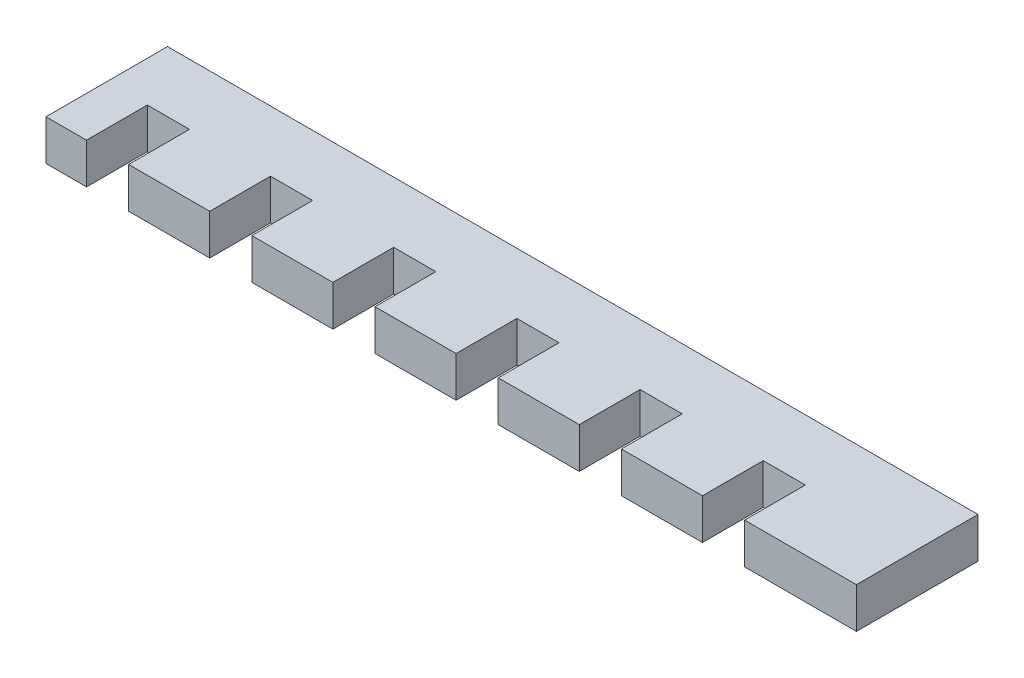
SolidWorks part; units mm, degrees
ref_plane "Front Plane" through (0, 0, 0) normal (0, 0, 1) x (1, 0, 0)
ref_plane "Top Plane" through (0, 0, 0) normal (0, 1, 0) x (1, 0, 0)
ref_plane "Right Plane" through (0, 0, 0) normal (1, 0, 0) x (0, 0, -1)
sketch "Sketch1" plane through (0, 0, 0) normal (0, 1, 0) x (1, 0, 0)
  line L1 (-50, 7.5) -> (50, 7.5)
  line L2 (-50, 7.5) -> (-50, -7.5)
  line L3 (-50, -7.5) -> (50, -7.5)
  line L4 (50, 7.5) -> (50, -7.5)
  line L5 (-50, 7.5) -> (50, -7.5) construction
  line L6 (-50, -7.5) -> (50, 7.5) construction
  point P0 (0, 0)
  dimension "D1" = 100
  dimension "D2" = 15
extrude "Boss-Extrude1" add sketch "Sketch1" along normal blind 5
sketch "Sketch2" plane through (0, 0, 0) normal (0, 1, 0) x (1, 0, 0)
  line L0 (-50, -7.5) -> (50, -7.5) construction
  line L1 (-45, -7.5) -> (-39.8, -7.5)
  line L2 (-45, -7.5) -> (-45, 0)
  line L3 (-45, 0) -> (-39.8, 0)
  line L4 (-39.8, -7.5) -> (-39.8, 0)
  line L5 (-50, 7.5) -> (-50, -7.5) construction
  line L8 (-29.8, -7.5) -> (-24.6, -7.5)
  line L9 (-29.8, -7.5) -> (-29.8, 0)
  line L10 (-29.8, 0) -> (-24.6, 0)
  line L11 (-24.6, -7.5) -> (-24.6, 0)
  line L12 (-14.6, -7.5) -> (-9.4, -7.5)
  line L13 (-14.6, -7.5) -> (-14.6, 0)
  line L14 (-14.6, 0) -> (-9.4, 0)
  line L15 (-9.4, -7.5) -> (-9.4, 0)
  line L16 (0.6, -7.5) -> (5.8, -7.5)
  line L17 (0.6, -7.5) -> (0.6, 0)
  line L18 (0.6, 0) -> (5.8, 0)
  line L19 (5.8, -7.5) -> (5.8, 0)
  line L20 (15.8, -7.5) -> (21, -7.5)
  line L21 (15.8, -7.5) -> (15.8, 0)
  line L22 (15.8, 0) -> (21, 0)
  line L23 (21, -7.5) -> (21, 0)
  line L24 (31, -7.5) -> (36.2, -7.5)
  line L25 (31, -7.5) -> (31, 0)
  line L26 (31, 0) -> (36.2, 0)
  line L27 (36.2, -7.5) -> (36.2, 0)
  dimension "D1" = 7.5
  dimension "D2" = 5
  dimension "D3" = 5.2
  dimension "D4" = 10
  dimension "D5" = 5.2
  dimension "D6" = 5.2
  dimension "D7" = 10
  dimension "D8" = 5.2
  dimension "D9" = 10
  dimension "D10" = 5.2
  dimension "D11" = 10
  dimension "D12" = 10
  dimension "D13" = 5.2
extrude "Cut-Extrude1" cut sketch "Sketch2" along normal blind 5
